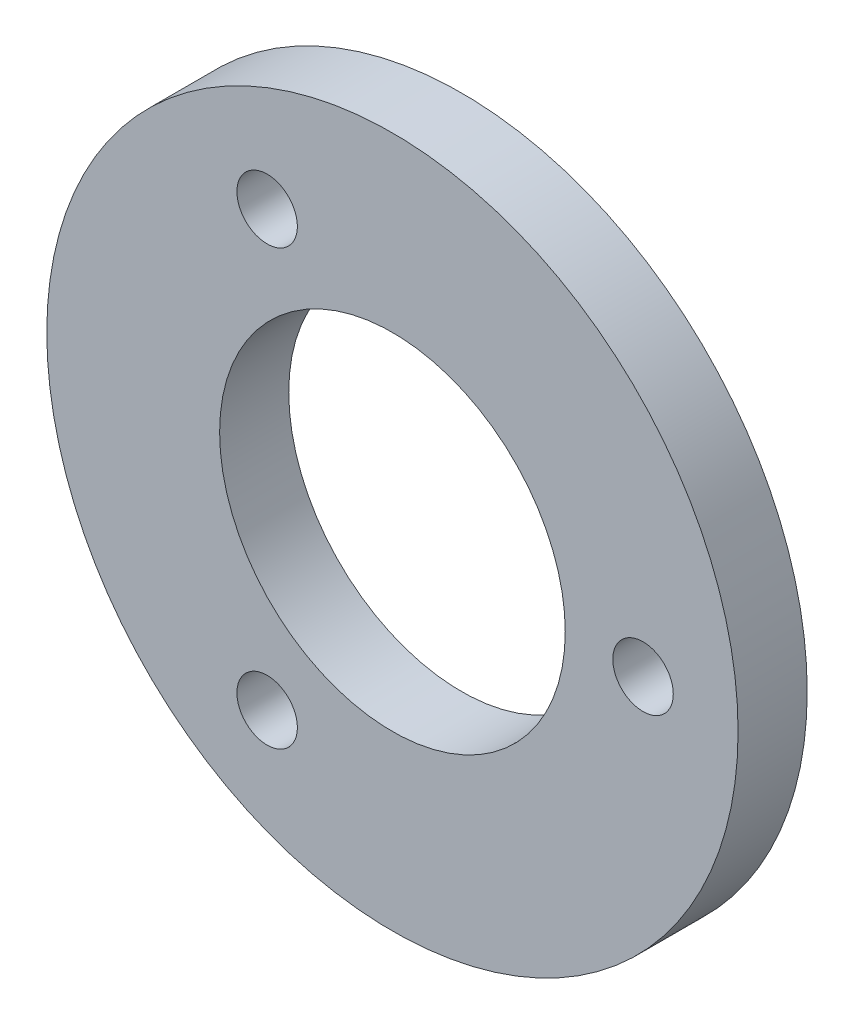
SolidWorks part; units mm, degrees
ref_plane "Front Plane" through (0, 0, 0) normal (0, 0, 1) x (1, 0, 0)
ref_plane "Top Plane" through (0, 0, 0) normal (0, 1, 0) x (1, 0, 0)
ref_plane "Right Plane" through (0, 0, 0) normal (1, 0, 0) x (0, 0, -1)
sketch "Sketch1" plane through (0, 0, 0) normal (0, 0, 1) x (1, 0, 0)
  circle A0 centre (0, 0) radius 10
  circle A1 centre (0, 0) radius 20
  circle A2 centre (14.5, 0) radius 1.75
  circle A3 centre (-7.25, -12.5574) radius 1.75
  circle A4 centre (-7.25, 12.5574) radius 1.75
  point P12 (0, 0)
  dimension "D1" = 20
  dimension "D2" = 40
  dimension "D3" = 3.5
  dimension "D4" = 14.5
  dimension "D6" = 7.25
  dimension "D7" = 12.5574
  dimension "D5" = 3
extrude "Boss-Extrude1" add sketch "Sketch1" along normal blind 4
